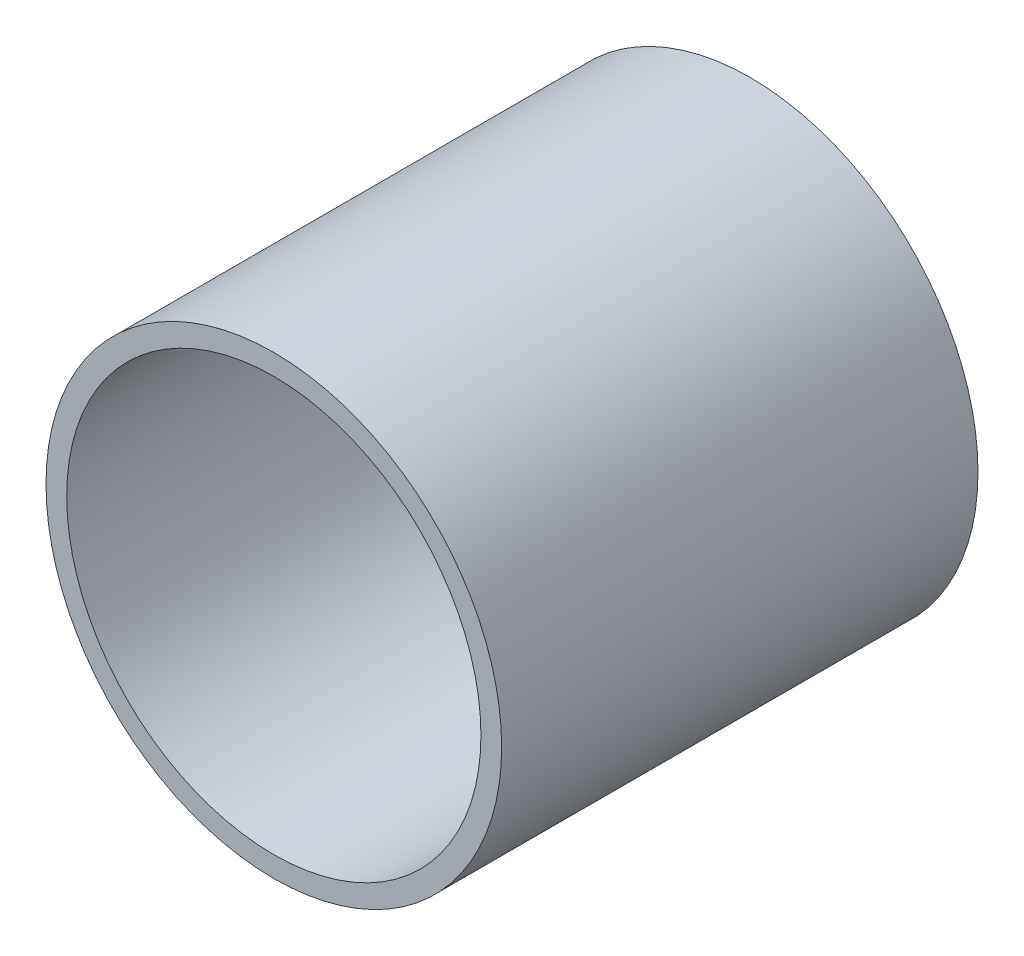
SolidWorks part; units mm, degrees
material "PLA"
ref_plane "Front Plane" through (0, 0, 0) normal (0, 0, 1) x (1, 0, 0)
ref_plane "Top Plane" through (0, 0, 0) normal (0, 1, 0) x (1, 0, 0)
ref_plane "Right Plane" through (0, 0, 0) normal (1, 0, 0) x (0, 0, -1)
sketch "Croquis1" plane through (0, 0, 0) normal (0, 0, 1) x (1, 0, 0)
  circle A0 centre (0, 0) radius 11
  circle A1 centre (0, 0) radius 10
  dimension "D1" = 22
  dimension "D2" = 20
extrude "Saliente-Extruir1" add sketch "Croquis1" along normal blind 23
